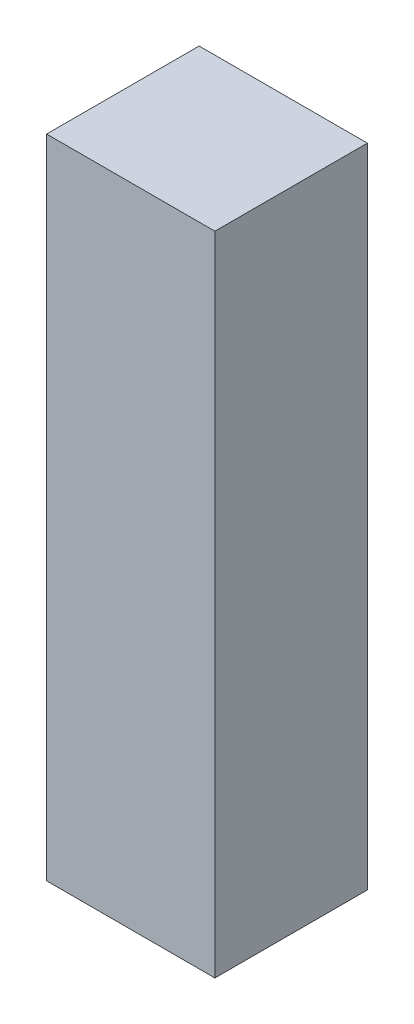
SolidWorks part; units mm, degrees
ref_plane "Front Plane" through (0, 0, 0) normal (1, 0, 0) x (0, 1, 0)
ref_plane "Top Plane" through (0, 0, 0) normal (0, 0, 1) x (0, 1, 0)
ref_plane "Right Plane" through (0, 0, 0) normal (0, 1, 0) x (-1, 0, 0)
sketch "Sketch2" plane through (0, 0, 0) normal (0, 0, 1) x (0, 1, 0)
  line L1 (31.242, -8.128) -> (-31.242, -8.128)
  line L2 (31.242, -8.128) -> (31.242, 8.128)
  line L3 (31.242, 8.128) -> (-31.242, 8.128)
  line L4 (-31.242, -8.128) -> (-31.242, 8.128)
  line L5 (31.242, -8.128) -> (-31.242, 8.128) construction
  line L6 (31.242, 8.128) -> (-31.242, -8.128) construction
  point P0 (0, 0)
  dimension "D1" = 62.484
  dimension "D2" = 16.256
extrude "Boss-Extrude1" add sketch "Sketch2" along normal blind 14.732
